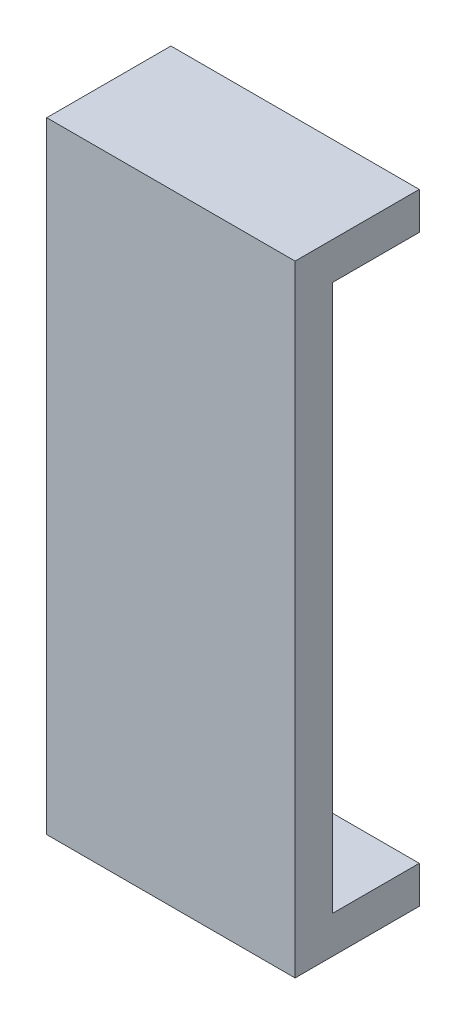
SolidWorks part; units mm, degrees
ref_plane "Alzado" through (0, 0, 0) normal (0, 0, 1) x (1, 0, 0)
ref_plane "Planta" through (0, 0, 0) normal (0, 1, 0) x (1, 0, 0)
ref_plane "Vista lateral" through (0, 0, 0) normal (1, 0, 0) x (0, 0, -1)
sketch "Croquis1" plane through (0, 0, 0) normal (0, 0, 1) x (1, 0, 0)
  line L1 (-10, 25) -> (10, 25)
  line L2 (-10, 25) -> (-10, -25)
  line L3 (-10, -25) -> (10, -25)
  line L4 (10, 25) -> (10, -25)
  line L5 (-10, 25) -> (10, -25) construction
  line L6 (-10, -25) -> (10, 25) construction
  point P0 (0, 0)
  dimension "D1" = 20
  dimension "D2" = 50
extrude "Saliente-Extruir1" add sketch "Croquis1" along normal blind 3
sketch "Croquis2" plane through (0, 0, 0) normal (0, 0, -1) x (-1, 0, 0)
  line L0 (10, 25) -> (10, -25) construction
  line L1 (-10, 25) -> (10, 25)
  line L2 (-10, 25) -> (-10, 22)
  line L3 (-10, 22) -> (10, 22)
  line L4 (10, 25) -> (10, 22)
  dimension "D1" = 3
extrude "Saliente-Extruir2" add sketch "Croquis2" along normal blind 7
sketch "Croquis3" plane through (0, 0, 0) normal (0, 0, -1) x (-1, 0, 0)
  line L0 (-10, -25) -> (-10, 22) construction
  line L1 (10, -25) -> (-10, -25)
  line L2 (10, -25) -> (10, -22)
  line L3 (10, -22) -> (-10, -22)
  line L4 (-10, -25) -> (-10, -22)
  dimension "D1" = 3
extrude "Saliente-Extruir3" add sketch "Croquis3" along normal blind 7
